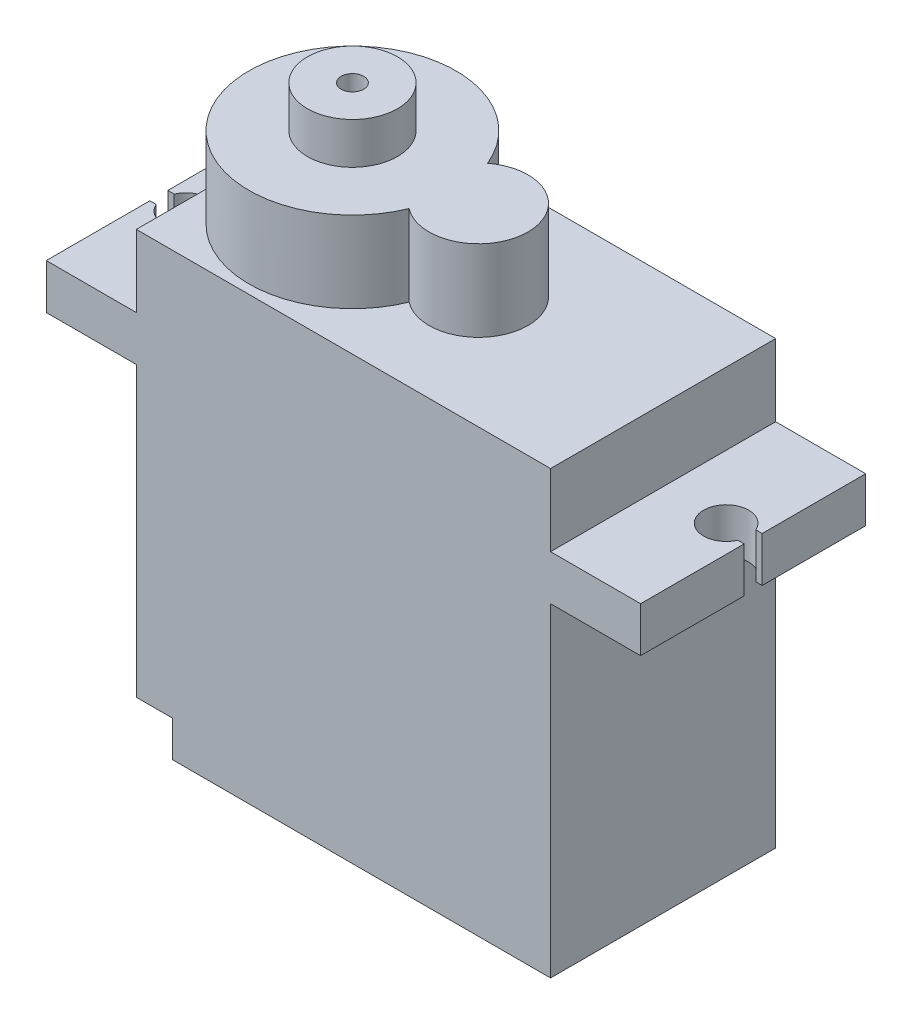
SolidWorks part; units mm, degrees
ref_plane "Front Plane" through (0, 0, 0) normal (0, 0, 1) x (1, 0, 0)
ref_plane "Top Plane" through (0, 0, 0) normal (0, 1, 0) x (1, 0, 0)
ref_plane "Right Plane" through (0, 0, 0) normal (1, 0, 0) x (0, 0, -1)
sketch "Sketch1" plane through (0, 0, 0) normal (0, 0, 1) x (1, 0, 0)
  line L2 (11.5, 9) -> (11.5, -9)
  line L3 (11.5, -9) -> (-11.5, -9)
  line L4 (-11.5, 9) -> (-11.5, -9)
  line L5 (11.5, 9) -> (-11.5, -9) construction
  line L6 (11.5, -9) -> (-11.5, 9) construction
  line L7 (-11.5, 9) -> (-16.5, 9)
  line L9 (-11.5, 11.5) -> (-16.5, 11.5)
  line L10 (-16.5, 9) -> (-16.5, 11.5)
  line L11 (11.5, 9) -> (16.5, 9)
  line L13 (11.5, 11.5) -> (16.5, 11.5)
  line L14 (16.5, 9) -> (16.5, 11.5)
  line L16 (-11.5, 11.5) -> (-11.5, 15.5)
  line L17 (-11.5, 15.5) -> (11.5, 15.5)
  line L18 (11.5, 11.5) -> (11.5, 15.5)
  point P0 (0, 0)
  dimension "D1" = 18
  dimension "D2" = 23
  dimension "D3" = 2.5
  dimension "D4" = 5
  dimension "D5" = 5
  dimension "D6" = 4
extrude "Boss-Extrude1" add sketch "Sketch1" along normal blind 12.5
sketch "Sketch2" plane through (0, 15.5, 0) normal (0, 1, 0) x (1, 0, 0)
  line L0 (-11.5, -12.5) -> (-11.5, 0) construction
  arc A0 (-0.4286, -4.0717) -> (-0.4286, -8.4283) centre (-5.75, -6.25) ccw
  arc A1 (-0.4286, -8.4283) -> (-0.4286, -4.0717) centre (1.25, -6.25) ccw
  dimension "D1" = 11.5
  dimension "D2" = 5.75
  dimension "D3" = 5.5
  dimension "D4" = 7
extrude "Boss-Extrude2" add sketch "Sketch2" along normal blind 4.5
chamfer "Chamfer1" distance 2 angle 45 1 edges at (-11.5, -9, 6.25)
sketch "Sketch3" plane through (0, -9, 0) normal (0, -1, 0) x (1, 0, 0)
  line L0 (-9.5, 12.5) -> (-9.5, 0) construction
  line L1 (-11.5, 0) -> (-9.5, 0)
  line L2 (-11.5, 0) -> (-11.5, 2)
  line L3 (-11.5, 2) -> (-9.5, 2)
  line L4 (-9.5, 0) -> (-9.5, 2)
  line L5 (-9.5, 10.5) -> (-9.5, 2) construction
  line L6 (-11.5, 12.5) -> (-9.5, 12.5)
  line L7 (-11.5, 12.5) -> (-11.5, 10.5)
  line L8 (-11.5, 10.5) -> (-9.5, 10.5)
  line L9 (-9.5, 12.5) -> (-9.5, 10.5)
  line L11 (-9.5, 8.15) -> (-11.5, 8.15)
  line L12 (-9.5, 8.15) -> (-9.5, 4.35)
  line L13 (-9.5, 4.35) -> (-11.5, 4.35)
  line L14 (-11.5, 8.15) -> (-11.5, 4.35)
  dimension "D1" = 2
  dimension "D2" = 2
  dimension "D3" = 3.8
  dimension "D4" = 2.35
extrude "Cut-Extrude1" cut sketch "Sketch3" against normal blind 2
sketch "Sketch4" plane through (0, 11.5, 0) normal (0, 1, 0) x (1, 0, 0)
  line L0 (16.5, -12.5) -> (16.5, 0) construction
  line L2 (16.1456, -6.75) -> (17.156, -6.75)
  line L3 (16.1456, -5.75) -> (17.156, -5.75)
  line L4 (17.156, -5.75) -> (17.156, -6.75)
  arc A0 (16.1456, -5.75) -> (16.1456, -6.75) centre (15, -6.25) ccw
  dimension "D1" = 2.5
  dimension "D2" = 1.5
extrude "Cut-Extrude2" cut sketch "Sketch4" against normal blind 5
ref_plane "Plane1" through (0, 0, 0) normal (-1, 0, 0) x (0, 0, 1)
mirror "Mirror1" about plane through (0, 0, 0) normal (-1, 0, 0) of "Cut-Extrude2"
sketch "Sketch5" plane through (0, 20, 0) normal (0, 1, 0) x (1, 0, 0)
  circle A0 centre (-5.75, -6.25) radius 2.5
  dimension "D1" = 5
extrude "Boss-Extrude3" add sketch "Sketch5" along normal blind 2.3
sketch "Sketch6" plane through (0, 22.3, 0) normal (0, 1, 0) x (1, 0, 0)
  circle A0 centre (-5.75, -6.25) radius 0.625
  dimension "D1" = 1.25
extrude "Cut-Extrude3" cut sketch "Sketch6" against normal up to surface (2.3 mm away) up to face at (-5.75, 20, 8.75)
sketch "Sketch7" plane through (0, 0, 12.5) normal (0, 0, 1) x (1, 0, 0)
  line L0 (-11.5, 17.75) -> (-18, 17.75)
  line L1 (-11.5, 20) -> (-11.5, 15.5) construction
  line L2 (-18, 17.75) -> (-18, -10.5)
  line L3 (-18, -10.5) -> (18, -10.5)
  line L4 (18, -10.5) -> (18, 17.75)
  line L5 (18, 17.75) -> (4, 17.75)
  line L6 (4, 15.5) -> (4, 20) construction
  line L9 (-9.5, -9) -> (11.5, -9) construction
  dimension "D1" = 6.5
  dimension "D2" = 14
  dimension "D3" = 1.5
